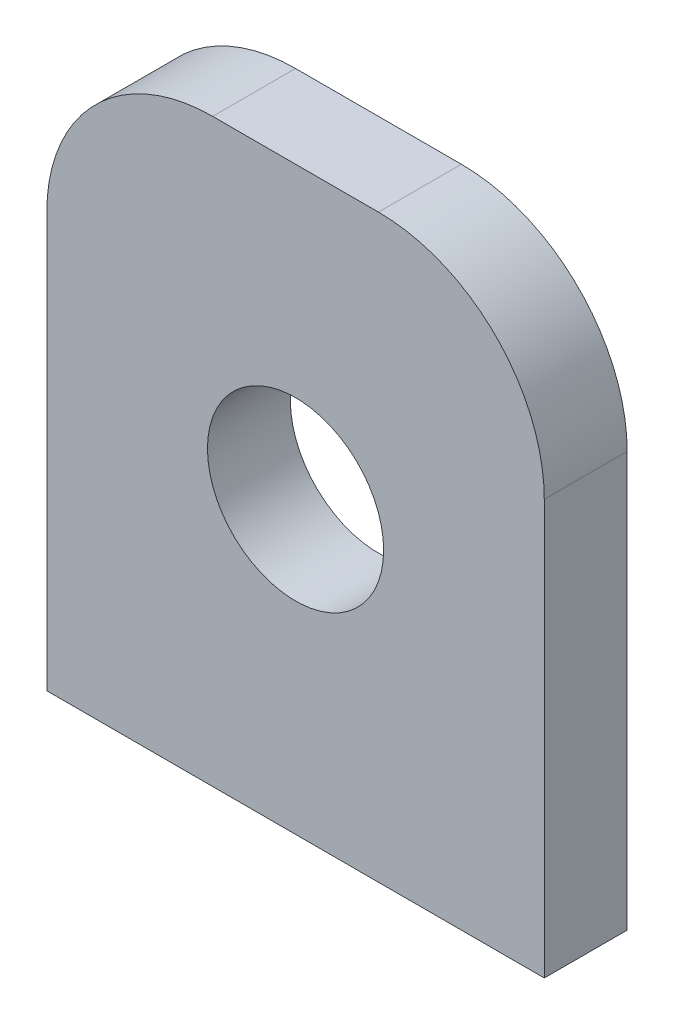
SolidWorks part; units mm, degrees
material "6061-T6 (SS)"
ref_plane "Front Plane" through (0, 0, 0) normal (0, 0, 1) x (1, 0, 0)
ref_plane "Top Plane" through (0, 0, 0) normal (0, 1, 0) x (1, 0, 0)
ref_plane "Right Plane" through (0, 0, 0) normal (1, 0, 0) x (0, 0, -1)
sketch "Sketch1" plane through (0, 0, 0) normal (0, 0, 1) x (1, 0, 0)
  line L1 (38.1, -44.45) -> (-38.1, -44.45)
  line L2 (38.1, -44.45) -> (38.1, 19.05)
  line L3 (12.7, 44.45) -> (-12.7, 44.45)
  line L4 (-38.1, -44.45) -> (-38.1, 19.05)
  line L5 (38.1, -44.45) -> (-38.1, 44.45) construction
  line L6 (38.1, 44.45) -> (-38.1, -44.45) construction
  arc A0 (38.1, 19.05) -> (12.7, 44.45) centre (12.7, 19.05) ccw
  arc A1 (-12.7, 44.45) -> (-38.1, 19.05) centre (-12.7, 19.05) ccw
  circle A2 centre (0, 0) radius 13.4938
  point P0 (0, 0)
  dimension "D1" = 25.4
  dimension "D4" = 26.9875
  dimension "D2" = 76.2
  dimension "D3" = 88.9
extrude "Boss-Extrude1" add sketch "Sketch1" along normal mid plane 12.7
sketch "Sketch2" plane through (0, -44.45, 0) normal (0, -1, 0) x (1, 0, 0)
  line L1 (19.05, -3.175) -> (-19.05, -3.175) construction
  line L2 (19.05, -3.175) -> (19.05, 3.175) construction
  line L3 (19.05, 3.175) -> (-19.05, 3.175) construction
  line L4 (-19.05, -3.175) -> (-19.05, 3.175) construction
  line L5 (19.05, -3.175) -> (-19.05, 3.175) construction
  line L6 (19.05, 3.175) -> (-19.05, -3.175) construction
  point P0 (0, 0)
  point P6 (-19.05, 0)
  point P7 (-19.05, 3.175)
  point P8 (19.05, 3.175)
  point P9 (19.05, -3.175)
  point P10 (-19.05, -3.175)
  point P11 (19.05, 0)
  dimension "D1" = 6.35
  dimension "D2" = 38.1
hole_wizard "#10-32 Tapped Hole1" positions "Sketch4" profile "Sketch3" tap size "#10-32" standard "ANSI Inch"
sketch "Sketch4" plane through (0, -44.45, 0) normal (0, -1, 0) x (-1, 0, 0)
  point P12 (19.05, 0)
  point P22 (-19.05, 0)
sketch "Sketch3" plane through (-19.05, -44.45, 0) normal (1, 0, 0) x (0, 0, -1)
  line L0 (0, 0) -> (0, 13.2428)
  line L1 (0, 13.2428) -> (2.0193, 12.0294)
  line L2 (2.0193, 12.0294) -> (2.0193, 0)
  line L5 (2.0193, 0) -> (0, 0)
  line L10 (0, 13.2428) -> (-2.0193, 12.0294) construction
  line L11 (0, -6.35) -> (0, 107.95) construction
  dimension "Tap Drill Dia." = 4.0386
  dimension "Tap Drill Depth" = 12.0294
  dimension "Drill Angle" = 118
cosmetic thread "Hole Thread1" parameters "D1"=9.652, "D2"=4.826
cosmetic thread "Hole Thread2" parameters "D1"=9.652, "D2"=4.826
